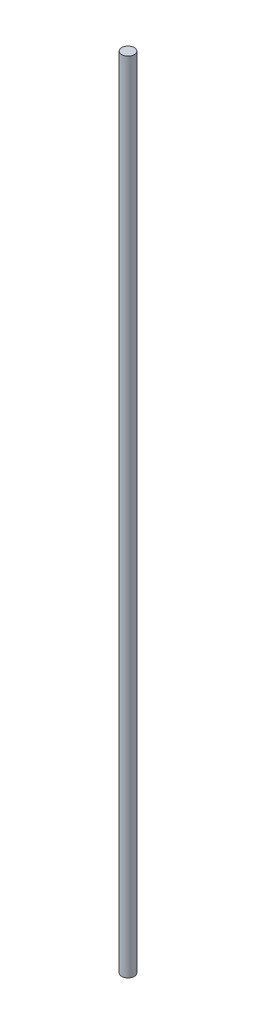
SolidWorks part; units mm, degrees
ref_plane "Front Plane" through (0, 0, 0) normal (0, 0, 1) x (1, 0, 0)
ref_plane "Top Plane" through (0, 0, 0) normal (0, 1, 0) x (1, 0, 0)
ref_plane "Right Plane" through (0, 0, 0) normal (1, 0, 0) x (0, 0, -1)
sketch "Sketch1" plane through (0, 0, 0) normal (0, 1, 0) x (1, 0, 0)
  circle A0 centre (0, 0) radius 19.05
extrude "Boss-Extrude1" add sketch "Sketch1" along normal blind 2438.4
